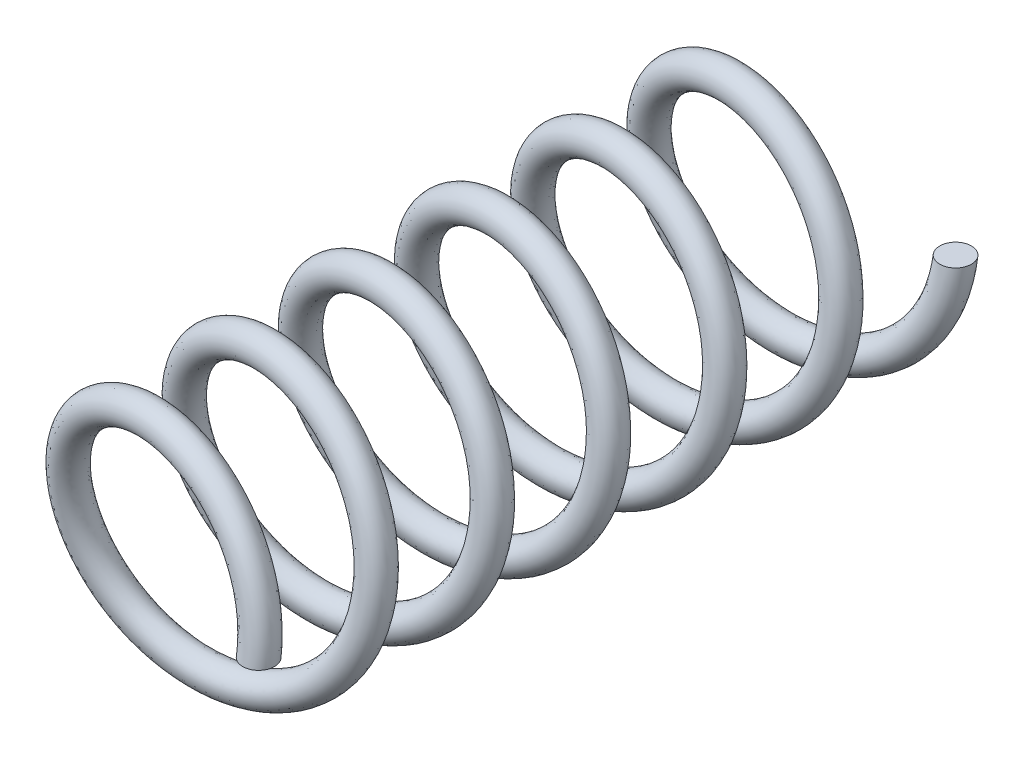
SolidWorks part; units mm, degrees
ref_plane "Front Plane" through (0, 0, 0) normal (0, 0, 1) x (1, 0, 0)
ref_plane "Top Plane" through (0, 0, 0) normal (0, 1, 0) x (1, 0, 0)
ref_plane "Right Plane" through (0, 0, 0) normal (1, 0, 0) x (0, 0, -1)
sketch "Sketch1" plane through (0, 0, 0) normal (0, 0, 1) x (1, 0, 0)
  circle A0 centre (0, 0) radius 24.765
  dimension "D1" = 49.53
curve "Helix/Spiral1" pitch 23.2833 height 139.7 turns 6
sketch "Sketch2" plane through (0, 0, 0) normal (0, 1, 0) x (1, 0, 0)
  circle A0 centre (24.765, -139.7) radius 3.175
  dimension "D1" = 6.35
sweep "Spring" add profiles "Sketch2" path "Helix/Spiral1"
